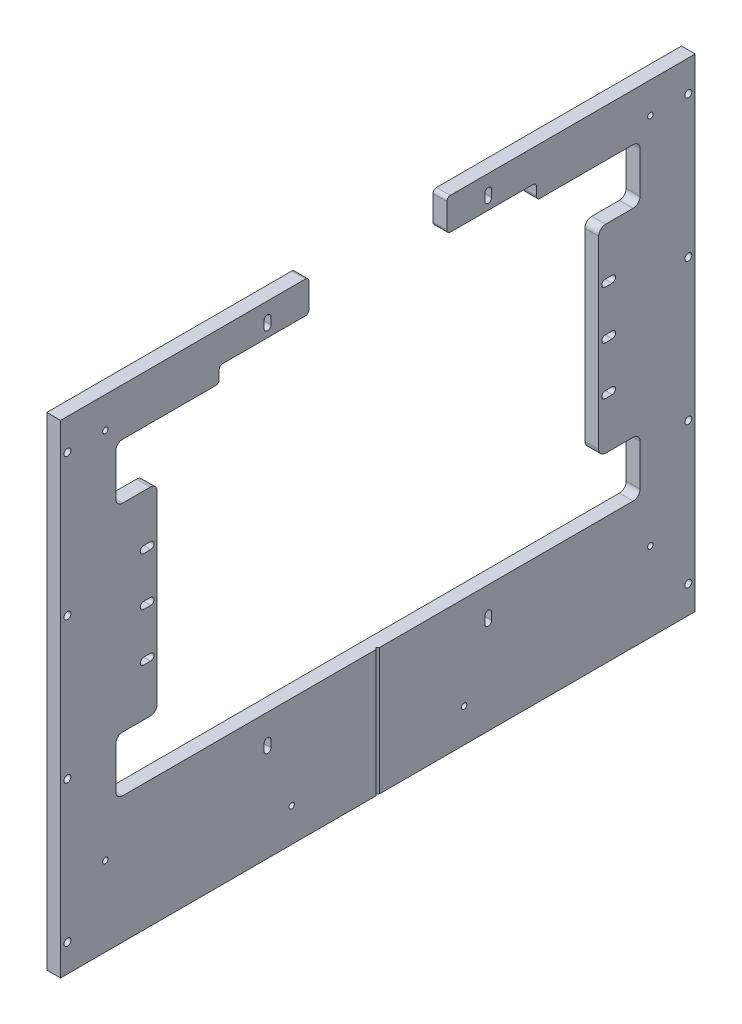
SolidWorks part; units mm, degrees
material "Alum 6061 (Default)"
ref_plane "Front Plane" through (0, 0, 0) normal (0, 0, 1) x (1, 0, 0)
ref_plane "Top Plane" through (0, 0, 0) normal (0, 1, 0) x (1, 0, 0)
ref_plane "Right Plane" through (0, 0, 0) normal (1, 0, 0) x (0, 0, -1)
sketch "Sketch10" plane through (-505.9553, 0, 0) normal (1, 0, 0) x (0, 0, -1)
  line L0 (-146.05, 36.5125) -> (146.05, 36.5125) construction
  line L1 (146.05, -80.1688) -> (-146.05, -80.1688)
  line L2 (146.05, -80.1688) -> (146.05, 153.1937)
  line L3 (146.05, 153.1937) -> (-146.05, 153.1937)
  line L4 (-146.05, -80.1688) -> (-146.05, 153.1937)
  line L5 (146.05, -80.1688) -> (-146.05, 153.1937) construction
  line L6 (146.05, 153.1937) -> (-146.05, -80.1688) construction
  point P0 (0, 36.5125)
  point P8 (0, 153.1937)
  dimension "D1" = 153.1937
  dimension "MainC" = 292.1
  dimension "MainD" = 233.3625
sketch "Sketch24" plane through (0, 0, 0) normal (1, 0, 0) x (0, 0, -1)
  line L1 (-146.05, -80.1688) -> (146.05, -80.1688)
  line L2 (-146.05, -80.1688) -> (-146.05, 153.1937)
  line L3 (-146.05, 153.1937) -> (146.05, 153.1937)
  line L4 (146.05, -80.1688) -> (146.05, 153.1937)
  line L5 (-146.05, -80.1688) -> (146.05, 153.1937) construction
  line L6 (-146.05, 153.1937) -> (146.05, -80.1688) construction
  point P0 (0, 36.5125)
sketch3d "3DSketch1"
  point P0 (0, 153.1937, 146.05)
  point P1 (0, -80.1688, 146.05)
  dimension "D2" = 146.05
  dimension "D1" = 146.05
sketch3d "3DSketch2"
  point P0 (0, 153.1937, -146.05)
  point P1 (0, -80.1688, -146.05)
  dimension "D2" = 146.05
  dimension "D1" = 146.05
sketch "Sketch1" plane through (0, 0, 0) normal (0, 0, 1) x (1, 0, 0)
  line L0 (0, -80.1688) -> (0, -222.25) construction
  line L1 (-6.35, 222.25) -> (6.35, 222.25)
  line L2 (-6.35, 222.25) -> (-6.35, -222.25)
  line L3 (-6.35, -222.25) -> (6.35, -222.25)
  line L4 (6.35, 222.25) -> (6.35, -222.25)
  line L5 (-6.35, 222.25) -> (6.35, -222.25) construction
  line L6 (-6.35, -222.25) -> (6.35, 222.25) construction
  point P0 (0, 0)
  point P2 (1.2269, 222.25)
  point P7 (0, -222.25)
  dimension "D1" = 69.0563
  dimension "Width" = 12.7
  dimension "D2" = 142.0812
extrude "Extrude1" add sketch "Sketch1" along normal up to surface (292.1 mm away) and the other way up to surface (292.1 mm away)
sketch "Sketch4" plane through (6.35, 0, 0) normal (1, 0, 0) x (0, 0, -1)
  line L0 (203.2, 127.7937) -> (241.3, 127.7937)
  line L2 (-203.2, 127.7937) -> (-203.2, -54.7688)
  line L3 (-241.3, -105.5688) -> (241.3, -105.5688)
  line L4 (203.2, 127.7937) -> (203.2, -54.7688)
  line L5 (-241.3, 178.5937) -> (241.3, 178.5937)
  line L6 (-241.3, 178.5937) -> (-241.3, 127.7937)
  line L7 (-241.3, 127.7937) -> (-203.2, 127.7937)
  line L8 (241.3, 178.5937) -> (241.3, 127.7937)
  line L9 (0, -105.5688) -> (0, 178.5937) construction
  line L10 (203.2, -54.7688) -> (241.3, -54.7688)
  line L11 (241.3, -54.7688) -> (241.3, -105.5688)
  line L12 (-203.2, -54.7688) -> (-241.3, -54.7688)
  line L13 (-241.3, -54.7688) -> (-241.3, -105.5688)
  line L17 (146.05, -80.1688) -> (146.05, 153.1937) construction
  line L19 (-146.05, -80.1688) -> (146.05, -80.1688) construction
  line L20 (-146.05, -80.1688) -> (-146.05, 153.1937) construction
  line L21 (292.1, 193.9593) -> (292.1, -82.6467) construction
  dimension "D2" = 57.15
  dimension "D3" = 50.8
  dimension "D4" = 50.8
  dimension "D5" = 25.4
  dimension "D6" = 25.4
  dimension "D7" = 25.4
  dimension "D8" = 57.15
extrude "Cut-Extrude1" cut sketch "Sketch4" against normal up to next
sketch "Sketch5" plane through (6.35, 0, 0) normal (1, 0, 0) x (0, 0, -1)
  line L6 (-63.5, 222.25) -> (-63.5, 178.5937)
  line L7 (-63.5, 178.5937) -> (63.5, 178.5937)
  line L8 (63.5, 222.25) -> (63.5, 178.5937)
  line L9 (-63.5, 222.25) -> (63.5, 222.25)
  line L17 (241.3, 178.5937) -> (-241.3, 178.5937) construction
  line L18 (88.9, 153.1937) -> (88.9, 205.8796) construction
  line L19 (-146.05, 153.1937) -> (146.05, 153.1937) construction
  line L20 (88.9, 205.8796) -> (63.5, 205.8796) construction
  line L27 (-292.1, 222.25) -> (292.1, 222.25) construction
  point P4 (0, 222.25)
  point P8 (0, 178.5937)
  dimension "D1" = 25.4
  dimension "D2" = 52.6859
  dimension "D3" = 82.55
extrude "Cut-Extrude2" cut sketch "Sketch5" against normal up to next
fillet "Fillet2" radius 6.35 12 edges at (0, 178.5937, 241.3) (0, 178.5937, -241.3) (0, 127.7937, -241.3) (0, 127.7937, 241.3) (0, 127.7937, -203.2) (0, 127.7937, 203.2) (0, -54.7688, 203.2) (0, -54.7688, -203.2) (0, -54.7688, -241.3) (0, -105.5688, -241.3) (0, -105.5688, 241.3) (0, -54.7688, 241.3)
hole_wizard "M6x1.0 Tapped Hole1" positions "Sketch9" profile "Sketch8" tap size "M6x1.0" standard "ANSI Metric" end condition up to next
sketch "Sketch9" plane through (6.35, 0, 0) normal (1, 0, 0) x (0, 0, -1)
  line L0 (-101.6, 204.7875) -> (101.6, 204.7875) construction
  line L5 (-101.6, -132.2388) -> (101.6, -132.2388) construction
  line L15 (146.05, 153.1937) -> (-146.05, 153.1937) construction
  line L16 (146.05, -80.1688) -> (-146.05, -80.1688) construction
  line L23 (-63.5, 222.25) -> (-63.5, 178.5937) construction
  line L24 (63.5, 178.5937) -> (63.5, 222.25) construction
  point P0 (101.6, 204.7875)
  point P2 (-101.6, 204.7875)
  point P17 (101.6, -132.2388)
  point P20 (-101.6, -132.2388)
  dimension "D2" = 51.5938
  dimension "D5" = 52.07
  dimension "D7" = 38.1
  dimension "D9" = 38.1
other "AlignGroup1"
sketch "Sketch8" plane through (6.35, 204.7875, -101.6) normal (0, 1, 0) x (0, 0, -1)
  line L0 (0, 0) -> (0, 12.7)
  line L1 (0, 12.7) -> (2.5, 12.7)
  line L2 (2.5, 12.7) -> (2.5, 0)
  line L5 (2.5, 0) -> (0, 0)
  line L11 (0, -6.35) -> (0, 107.95) construction
  dimension "Thru Tap Drill Dia." = 5
  dimension "Thru Tap Drill Depth" = 12.7
cosmetic thread "Hole Thread11" parameters "D2"=6
cosmetic thread "Hole Thread12" parameters "D2"=6
cosmetic thread "Hole Thread41" parameters "D2"=6
cosmetic thread "Hole Thread42" parameters "D2"=6
sketch "Sketch11" plane through (6.35, 0, 0) normal (1, 0, 0) x (0, 0, -1)
  line L0 (234.95, 178.5937) -> (63.5, 178.5937) construction
  line L1 (-146.05, 178.5937) -> (146.05, 178.5937)
  line L2 (-146.05, 178.5937) -> (-146.05, 192.8812)
  line L3 (-146.05, 192.8812) -> (146.05, 192.8812)
  line L4 (146.05, 178.5937) -> (146.05, 192.8812)
  line L5 (292.1, 193.9593) -> (292.1, -82.6467) construction
  circle A0 centre (-101.6, 204.7875) radius 2.5 construction
  point P6 (0, 178.5937)
  dimension "D2" = 11.9062
  dimension "D3" = 146.05
extrude "Cut-Extrude3" cut sketch "Sketch11" against normal through all
fillet "Fillet3" radius 3.175 8 edges at (0, 222.25, -63.5) (0, 222.25, 63.5) (0, 178.5937, -146.05) (0, 192.8812, -146.05) (0, 178.5937, 146.05) (0, 192.8812, -63.5) (0, 192.8812, 63.5) (0, 192.8812, 146.05)
sketch "Sketch18" plane through (0, -222.25, 0) normal (0, -1, 0) x (1, 0, 0)
  line L3 (6.35, 1.5875) -> (6.35, -1.5875)
  line L4 (6.35, -1.5875) -> (4.7625, 0)
  line L5 (4.7625, 0) -> (6.35, 1.5875)
  line L6 (6.35, 292.1) -> (6.35, -292.1) construction
  point P2 (6.35, 0)
  dimension "D1" = 3.175
  dimension "D2" = 1.5875
extrude "Cut-Extrude7" cut sketch "Sketch18" against normal through all both and the other way through all
sketch "Sketch19" plane through (6.35, 0, 0) normal (1, 0, 0) x (0, 0, -1)
  line L12 (101.6, 207.9625) -> (101.6, 201.6125) construction
  line L13 (104.775, 207.9625) -> (104.775, 201.6125)
  line L14 (98.425, 207.9625) -> (98.425, 201.6125)
  line L15 (-101.6, 207.9625) -> (-101.6, 201.6125) construction
  line L16 (-98.425, 207.9625) -> (-98.425, 201.6125)
  line L17 (-104.775, 207.9625) -> (-104.775, 201.6125)
  line L18 (-101.6, -129.0638) -> (-101.6, -135.4138) construction
  line L19 (-98.425, -129.0638) -> (-98.425, -135.4138)
  line L20 (-104.775, -129.0638) -> (-104.775, -135.4138)
  line L21 (101.6, -129.0638) -> (101.6, -135.4138) construction
  line L22 (104.775, -129.0638) -> (104.775, -135.4138)
  line L23 (98.425, -129.0638) -> (98.425, -135.4138)
  arc A8 (104.775, 207.9625) -> (98.425, 207.9625) centre (101.6, 207.9625) ccw
  arc A9 (98.425, 201.6125) -> (104.775, 201.6125) centre (101.6, 201.6125) ccw
  arc A10 (-98.425, 207.9625) -> (-104.775, 207.9625) centre (-101.6, 207.9625) ccw
  arc A11 (-104.775, 201.6125) -> (-98.425, 201.6125) centre (-101.6, 201.6125) ccw
  arc A12 (-98.425, -129.0638) -> (-104.775, -129.0638) centre (-101.6, -129.0638) ccw
  arc A13 (-104.775, -135.4138) -> (-98.425, -135.4138) centre (-101.6, -135.4138) ccw
  arc A14 (104.775, -129.0638) -> (98.425, -129.0638) centre (101.6, -129.0638) ccw
  arc A15 (98.425, -135.4138) -> (104.775, -135.4138) centre (101.6, -135.4138) ccw
  point P33 (101.6, 204.7875)
  point P41 (-101.6, 204.7875)
  point P49 (-101.6, -132.2388)
  point P57 (101.6, -132.2388)
  dimension "D1" = 6.35
  dimension "D2" = 6.35
extrude "Cut-Extrude8" cut sketch "Sketch19" against normal up to next
hole_wizard "M6x1.0 Tapped Hole2" positions "Sketch20" profile "Sketch21" tap size "M6x1.0" standard "ANSI Metric" end condition up to next
sketch "Sketch20" plane through (6.35, 0, 0) normal (1, 0, 0) x (0, 0, -1)
  line L0 (-146.05, -80.1688) -> (-146.05, 153.1937) construction
  line L1 (146.05, -80.1688) -> (146.05, 153.1937) construction
  line L3 (-250.825, 193.675) -> (-250.825, -149.225) construction
  line L5 (-250.825, 22.225) -> (-170.837, 22.225) construction
  line L9 (-79.375, -191.2938) -> (79.375, -191.2938) construction
  line L11 (-292.1, 125.73) -> (-292.1, -125.73) construction
  line L12 (-146.05, -80.1688) -> (146.05, -80.1688) construction
  point P0 (79.375, -191.2938)
  point P3 (-79.375, -191.2938)
  point P6 (250.825, -149.225)
  point P9 (250.825, 193.675)
  point P12 (-250.825, 193.675)
  point P15 (-250.825, -149.225)
  point P43 (0, -191.2938)
  dimension "D1" = 104.775
  dimension "D2" = 104.775
  dimension "D3" = 40.4813
  dimension "D5" = 212.725
  dimension "D6" = 111.125
  dimension "D7" = 69.0562
sketch "Sketch21" plane through (6.35, -191.2938, -79.375) normal (0, 1, 0) x (0, 0, -1)
  line L0 (0, 0) -> (0, 12.7)
  line L1 (0, 12.7) -> (2.5, 12.7)
  line L2 (2.5, 12.7) -> (2.5, 0)
  line L5 (2.5, 0) -> (0, 0)
  line L11 (0, -6.35) -> (0, 107.95) construction
  dimension "Thru Tap Drill Dia." = 5
  dimension "Thru Tap Drill Depth" = 12.7
cosmetic thread "Hole Thread39" parameters "D2"=6
cosmetic thread "Hole Thread40" parameters "D2"=6
cosmetic thread "Hole Thread44" parameters "D2"=6
cosmetic thread "Hole Thread45" parameters "D2"=6
cosmetic thread "Hole Thread48" parameters "D2"=6
cosmetic thread "Hole Thread49" parameters "D2"=6
hole_wizard "M6 Clearance Hole1" positions "Sketch22" profile "Sketch23" hole size "M6" standard "ANSI Metric" end condition up to next
sketch "Sketch22" plane through (6.35, 0, 0) normal (1, 0, 0) x (0, 0, -1)
  line L0 (-292.1, 222.25) -> (-66.675, 222.25) construction
  line L1 (-292.1, -222.25) -> (-292.1, 222.25) construction
  line L2 (292.1, -222.25) -> (292.1, 222.25) construction
  line L3 (-292.1, -222.25) -> (292.1, -222.25) construction
  line L4 (-285.75, 193.675) -> (-285.75, 63.5) construction
  line L5 (-285.75, 63.5) -> (-285.75, -66.675) construction
  line L6 (-285.75, -66.675) -> (-285.75, -196.85) construction
  point P0 (-285.75, -196.85)
  point P2 (-285.75, -66.675)
  point P4 (-285.75, 193.675)
  point P6 (-285.75, 63.5)
  point P15 (285.75, 193.675)
  point P17 (285.75, 63.5)
  point P19 (285.75, -66.675)
  point P21 (285.75, -196.85)
  dimension "D1" = 28.575
  dimension "D5" = 6.35
  dimension "D6" = 6.35
  dimension "D7" = 25.4
sketch "Sketch23" plane through (6.35, -196.85, 285.75) normal (0, 1, 0) x (0, 0, -1)
  line L0 (0, 0) -> (0, 12.7)
  line L1 (0, 12.7) -> (3.2, 12.7)
  line L2 (3.2, 12.7) -> (3.2, 0)
  line L5 (3.2, 0) -> (0, 0)
  line L11 (0, -6.35) -> (0, 107.95) construction
  dimension "Thru Hole Dia." = 6.4
  dimension "Thru Hole Depth" = 12.7
sketch "Sketch25" plane through (-6.35, 0, 0) normal (-1, 0, 0) x (0, 0, 1)
  point P0 (250.825, 193.675)
  point P1 (250.825, -149.225)
sketch "Sketch26" plane through (-6.35, 0, 0) normal (-1, 0, 0) x (0, 0, 1)
  arc A0 (-98.425, 207.9625) -> (-104.775, 207.9625) centre (-101.6, 207.9625) ccw construction
  arc A1 (104.775, 207.9625) -> (98.425, 207.9625) centre (101.6, 207.9625) ccw construction
  point P0 (-101.6, 211.1375)
  point P1 (101.6, 211.1375)
sketch "Sketch27" plane through (-6.35, 0, 0) normal (-1, 0, 0) x (0, 0, 1)
  line L0 (-212.4075, 153.1937) -> (-212.4075, -80.1688) construction
  line L2 (-203.2, 121.4437) -> (-203.2, -48.4188) construction
  line L3 (-209.2325, 36.5125) -> (-215.5825, 36.5125) construction
  line L4 (-209.2325, 33.3375) -> (-215.5825, 33.3375)
  line L5 (-209.2325, 39.6875) -> (-215.5825, 39.6875)
  line L6 (0, 153.1937) -> (0, -80.1688) construction
  line L7 (146.05, 153.1937) -> (-146.05, 153.1937) construction
  line L8 (146.05, -80.1688) -> (-146.05, -80.1688) construction
  arc A1 (-209.2325, 33.3375) -> (-209.2325, 39.6875) centre (-209.2325, 36.5125) ccw
  arc A2 (-215.5825, 39.6875) -> (-215.5825, 33.3375) centre (-215.5825, 36.5125) ccw
  point P8 (-212.4075, 36.5125)
  dimension "D2" = 3.175
  dimension "D1" = 9.2075
  dimension "D3" = 6.35
extrude "Cut-Extrude9" cut sketch "Sketch27" against normal through all
sketch "Sketch28" plane through (-6.35, 0, 0) normal (-1, 0, 0) x (0, 0, 1)
  line L0 (0, 153.1937) -> (0, 0) construction
  line L1 (146.05, 153.1937) -> (-146.05, 153.1937) construction
mirror "Mirror1" about plane through (0, 0, 0) normal (0, 0, 1) of "Cut-Extrude9"
sketch "Sketch29" plane through (6.35, 0, 0) normal (1, 0, 0) x (0, 0, -1)
  line L0 (-215.5825, 80.9625) -> (-209.2325, 80.9625) construction
  line L1 (-215.5825, 84.1375) -> (-209.2325, 84.1375)
  line L2 (-215.5825, 77.7875) -> (-209.2325, 77.7875)
  line L3 (-215.5825, -7.9375) -> (-209.2325, -7.9375) construction
  line L4 (-215.5825, -4.7625) -> (-209.2325, -4.7625)
  line L5 (-215.5825, -11.1125) -> (-209.2325, -11.1125)
  line L6 (-212.4075, 80.9625) -> (-212.4075, 36.5125) construction
  line L7 (-209.2325, 39.6875) -> (-215.5825, 39.6875) construction
  line L8 (-212.4075, 36.5125) -> (-212.4075, -7.9375) construction
  line L9 (-218.7575, 36.5125) -> (-206.0575, 36.5125) construction
  line L10 (-234.95, 127.7937) -> (-209.55, 127.7937) construction
  arc A0 (-215.5825, 84.1375) -> (-215.5825, 77.7875) centre (-215.5825, 80.9625) ccw
  arc A1 (-209.2325, 77.7875) -> (-209.2325, 84.1375) centre (-209.2325, 80.9625) ccw
  arc A2 (-215.5825, -4.7625) -> (-215.5825, -11.1125) centre (-215.5825, -7.9375) ccw
  arc A3 (-209.2325, -11.1125) -> (-209.2325, -4.7625) centre (-209.2325, -7.9375) ccw
  arc A4 (-215.5825, 39.6875) -> (-215.5825, 33.3375) centre (-215.5825, 36.5125) ccw construction
  arc A5 (-209.2325, 33.3375) -> (-209.2325, 39.6875) centre (-209.2325, 36.5125) ccw construction
  point P2 (-212.4075, 80.9625)
  point P7 (-212.4075, -7.9375)
  dimension "D2" = 46.8313
extrude "Cut-Extrude10" cut sketch "Sketch29" against normal through all
mirror "Mirror2" about plane through (0, 0, 0) normal (0, 0, 1) of "Cut-Extrude10"
